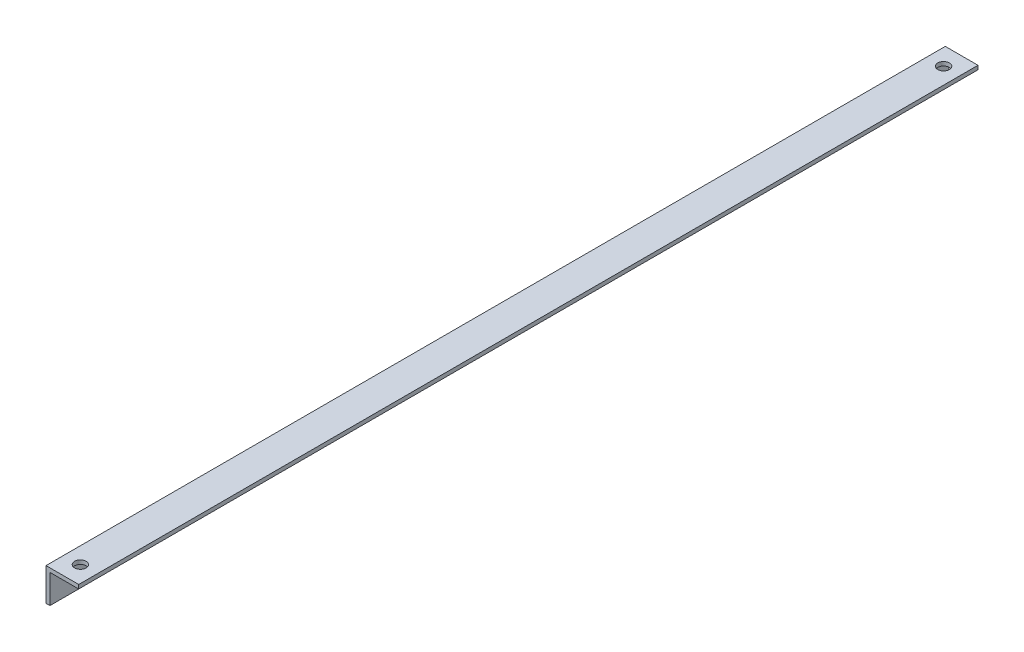
SolidWorks part; units mm, degrees
ref_plane "Front Plane" through (0, 0, 0) normal (0, 0, 1) x (1, 0, 0)
ref_plane "Top Plane" through (0, 0, 0) normal (0, 1, 0) x (1, 0, 0)
ref_plane "Right Plane" through (0, 0, 0) normal (1, 0, 0) x (0, 0, -1)
sketch "Sketch1" plane through (0, 0, 0) normal (0, 0, 1) x (1, 0, 0)
  line L0 (0, 0) -> (12.7, 0)
  line L1 (12.7, 0) -> (12.7, -1.524)
  line L2 (12.7, -1.524) -> (1.524, -1.524)
  line L3 (1.524, -1.524) -> (1.524, -12.7)
  line L4 (1.524, -12.7) -> (0, -12.7)
  line L5 (0, -12.7) -> (0, 0)
  dimension "D1" = 12.7
  dimension "D2" = 1.524
extrude "Boss-Extrude1" add sketch "Sketch1" along normal blind 349
hole_wizard "M4 Clearance Hole1" positions "Sketch2" profile "Sketch3" hole size "M4" standard "ANSI Metric" end condition through all
sketch "Sketch2" plane through (0, 0, 0) normal (0, 1, 0) x (1, 0, 0)
  line L0 (6.35, -7) -> (6.35, 0) construction
  line L1 (12.7, 0) -> (0, 0) construction
  line L2 (0, -174.5) -> (12.7, -174.5) construction
  line L3 (0, -349) -> (0, 0) construction
  line L4 (12.7, -349) -> (12.7, 0) construction
  point P0 (6.35, -7)
  point P2 (6.35, -342)
  point P21 (0, 0)
  dimension "D1" = 335
sketch "Sketch3" plane through (6.35, 0, 7) normal (1, 0, 0) x (0, 0, 1)
  line L0 (0, 0) -> (0, 12.7)
  line L1 (0, 12.7) -> (2.25, 12.7)
  line L2 (2.25, 12.7) -> (2.25, 0)
  line L5 (2.25, 0) -> (0, 0)
  line L11 (0, -6.35) -> (0, 107.95) construction
  dimension "Thru Hole Dia." = 4.5
  dimension "Thru Hole Depth" = 12.7
hole_wizard "M4x0.7 Tapped Hole1" positions "Sketch4" profile "Sketch5" tap size "M4x0.7" standard "ANSI Metric" end condition through all
sketch "Sketch4" plane through (0, 0, 0) normal (-1, 0, 0) x (0, 0, 1)
  line L0 (349, 0) -> (0, 0) construction
  line L4 (174.5, 0) -> (174.5, -12.7) construction
  line L5 (349, -12.7) -> (0, -12.7) construction
  point P0 (65.554, -6.35)
  point P10 (283.446, -6.35)
  dimension "D1" = 6.35
  dimension "D2" = 217.8921
sketch "Sketch5" plane through (0, -6.35, 65.554) normal (0, 1, 0) x (0, 0, 1)
  line L0 (0, 0) -> (0, 12.7)
  line L1 (0, 12.7) -> (1.65, 12.7)
  line L2 (1.65, 12.7) -> (1.65, 0)
  line L5 (1.65, 0) -> (0, 0)
  line L11 (0, -6.35) -> (0, 107.95) construction
  dimension "Thread Major Dia." = 3.3
  dimension "Thru Tap Drill Depth" = 12.7
